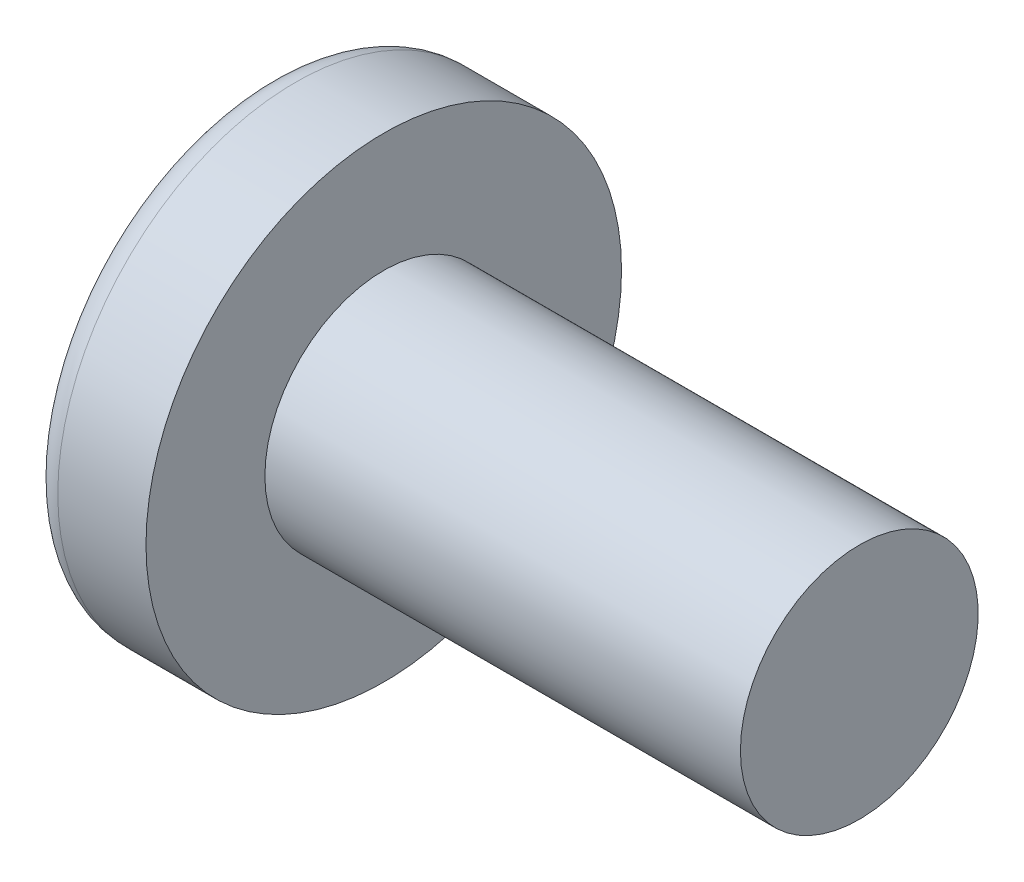
SolidWorks part; units mm, degrees
ref_plane "Plane1" through (0, 0, 0) normal (0, 0, 1) x (1, 0, 0)
ref_plane "Plane2" through (0, 0, 0) normal (0, 1, 0) x (1, 0, 0)
ref_plane "Plane3" through (0, 0, 0) normal (1, 0, 0) x (0, 0, -1)
sketch "BodySke" plane through (0, 0, 0) normal (0, 0, 1) x (1, 0, 0)
  line L0 (3.1, 2) -> (3.1, 4)
  line L1 (3.8, 6.35) -> (3.8, -3.175) construction
  line L2 (-25.4, 0) -> (127, 0) construction
  line L3 (11.1, 0) -> (0, 0)
  line L4 (3.1, 2) -> (11.1, 2)
  line L5 (11.1, 2) -> (11.1, 0)
  line L6 (1.6164, 4) -> (3.1, 4)
  line L7 (3.1, -2) -> (11.1, -2) construction
  line L8 (3.1, 6.35) -> (3.1, -3.175) construction
  arc A0 (1.227, 3.8007) -> (0, 0) centre (6.5, 0) ccw
  arc A2 (1.227, 3.8007) -> (1.6164, 4) centre (1.6164, 3.52) cw
  dimension "Head_crown_rad" = 6.5
  dimension "Head_fillet_rad" = 0.48
  dimension "Diameter" = 4
  dimension "Length" = 8
  dimension "Head_ht" = 3.1
  dimension "Head_dia" = 8
  dimension "Advance" = 0.7
  dimension "Thread_nom" = 8
revolve "Base-Revolve" add sketch "BodySke" angle 360 about L2
cosmetic thread "ThreadCosmetic" [suppressed] parameters "Thread_length"=7.3, "Thread_minor"=3.22
sketch "Sketch3" plane through (0, 0, 0) normal (1, 0, 0) x (0, 0, -1)
  line L0 (0.465, -2.2) -> (-0.465, -2.2)
  line L1 (0.465, -2.2) -> (0.465, 2.2)
  line L2 (-0.465, 2.2) -> (0.465, 2.2)
  line L3 (-0.465, 2.2) -> (-0.465, -2.2)
  dimension "Cross_dia" = 4.4
  dimension "D1" = 2.2
  dimension "Cross_width" = 0.93
  dimension "D2" = 0.465
ref_plane "Plane4" through (2.45, 0, 0) normal (1, 0, 0) x (0, 0, -1)
sketch "Sketch4" plane through (2.45, 0, 0) normal (1, 0, 0) x (0, 0, -1)
  line L0 (0.2325, -0.2325) -> (-0.2325, -0.2325)
  line L1 (0.2325, -0.2325) -> (0.2325, 0.2325)
  line L2 (-0.2325, 0.2325) -> (0.2325, 0.2325)
  line L3 (-0.2325, 0.2325) -> (-0.2325, -0.2325)
  dimension "D2" = 0.465
  dimension "D1" = 0.465
  dimension "D3" = 0.2325
  dimension "D4" = 0.2325
loft "Cut-Loft1" cut profiles "Sketch3", "Sketch4"
pattern_circular "CirPattern1" count 2 every 90 about axis through (0, 0, 0) along (1, 0, 0) of "Cut-Loft1"
sketch "ThdSchSke" plane through (0, 0, 0) normal (0, 0, 1) x (1, 0, 0)
  line L0 (3.8, -1.61) -> (3.5269, -2)
  line L1 (3.8, -1.61) -> (4.0731, -2)
  line L2 (4.0731, -2) -> (4.0731, -2.5)
  line L3 (-3.175, 0) -> (5.1513, 0) construction
  line L5 (4.0731, -2.5) -> (3.5269, -2.5)
  line L6 (3.5269, -2.5) -> (3.5269, -2)
  dimension "Diameter" = 4
  dimension "SideAngle" = 55
  dimension "VeeAngle" = 70
  dimension "Thread_minor" = 3.22
  dimension "Overcut" = 5
  dimension "Start" = 3.8
revolve "ThreadSchematic" [suppressed] cut sketch "ThdSchSke" angle 360 about L3
pattern_linear "ThdSchPat" [suppressed]
equation "\"D1@Sketch3\" = \"Cross_dia@Sketch3\" / 2"
equation "\"D2@Sketch3\" = \"Cross_width@Sketch3\" / 2"
equation "\"D1@Sketch4\" = \"Cross_width@Sketch3\" *.5"
equation "\"D2@Sketch4\" = \"D1@Sketch4\""
equation "\"D3@Sketch4\" = \"D1@Sketch4\" / 2"
equation "\"D4@Sketch4\" = \"D2@Sketch4\" / 2"
equation "\"Thread_length@ThreadCosmetic\" = ((sgn( (\"Length@BodySke\" - \"Advance@BodySke\" ) - \"Thread_nom@BodySke\" )-1)*( (\"Length@BodySke\" - \"Advance@BodySke\" ) - \"Thread_nom@BodySke\" ))/-2+ \"Thread_nom@BodySke\""
equation "\"Thread_minor@ThdSchSke\" = \"Thread_minor@ThreadCosmetic\""
equation "\"Diameter@ThdSchSke\" = \"Diameter@BodySke\""
equation "\"Overcut@ThdSchSke\" = \"Diameter@BodySke\" * 1.25"
equation "\"Start@ThdSchSke\" = \"Head_ht@BodySke\" + \"Length@BodySke\" - \"Thread_length@ThreadCosmetic\"  '---Non-countersunk---"
equation "\"Num_threads@ThdSchPat\" = int( \"Thread_length@ThreadCosmetic\" / \"Advance@BodySke\" + 0.999 )  + 1"
equation "\"Advance@ThdSchPat\" = \"Thread_length@ThreadCosmetic\" /  (\"Num_threads@ThdSchPat\" - 1) 'relax it"
